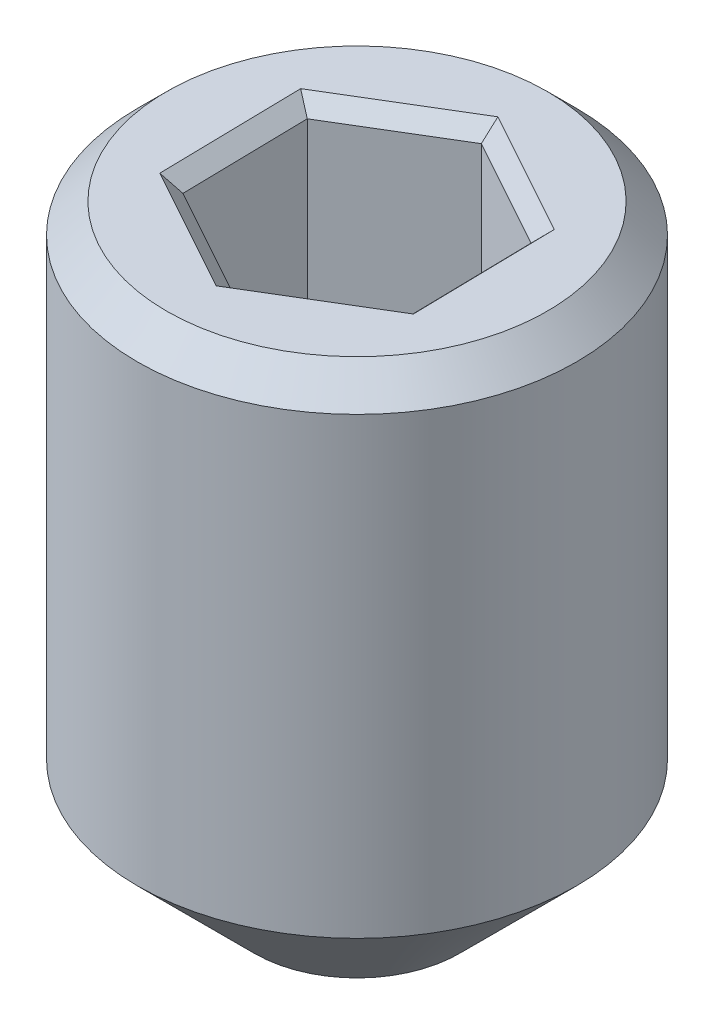
SolidWorks part; units mm, degrees
material "Plain Carbon Steel"
ref_plane "Front Plane" through (0, 0, 0) normal (0, 0, 1) x (1, 0, 0)
ref_plane "Top Plane" through (0, 0, 0) normal (0, 1, 0) x (1, 0, 0)
ref_plane "Right Plane" through (0, 0, 0) normal (1, 0, 0) x (0, 0, -1)
sketch "Sketch1" plane through (0, 0, 0) normal (0, 1, 0) x (1, 0, 0)
  circle A0 centre (0, 0) radius 1.5
  dimension "D1" = 3
extrude "Boss-Extrude1" add sketch "Sketch1" along normal blind 4.1
sketch "Sketch2" plane through (0, 4.1, 0) normal (0, 1, 0) x (1, 0, 0)
  line L1 (0.7582, -0.4185) -> (0.7415, 0.4474)
  line L2 (0.7415, 0.4474) -> (-0.0167, 0.8659)
  line L3 (-0.0167, 0.8659) -> (-0.7582, 0.4185)
  line L4 (-0.7582, 0.4185) -> (-0.7415, -0.4474)
  line L5 (-0.7415, -0.4474) -> (0.0167, -0.8659)
  line L6 (0.0167, -0.8659) -> (0.7582, -0.4185)
  circle A0 centre (0, 0) radius 0.75 construction
  dimension "D1" = 1.5
extrude "Cut-Extrude2" cut sketch "Sketch2" against normal blind 2
chamfer "Chamfer1" distance 0.2 angle 45 1 edges at (0, 4.1, 1.5)
chamfer "Chamfer2" distance 0.1 angle 45 6 edges at (-0.7499, 4.1, 0.0144) (-0.3624, 4.1, 0.6566) (0.3874, 4.1, 0.6422) (0.7499, 4.1, -0.0144) (0.3624, 4.1, -0.6566) (-0.3874, 4.1, -0.6422)
fillet "Fillet3" radius 0.6 6 edges at (-0.7499, 2.1, 0.0144) (-0.3624, 2.1, 0.6566) (0.3874, 2.1, 0.6422) (0.7499, 2.1, -0.0144) (0.3624, 2.1, -0.6566) (-0.3874, 2.1, -0.6422)
chamfer "Chamfer3" distance 0.8 angle 45 1 edges at (0, 0, 1.5)
